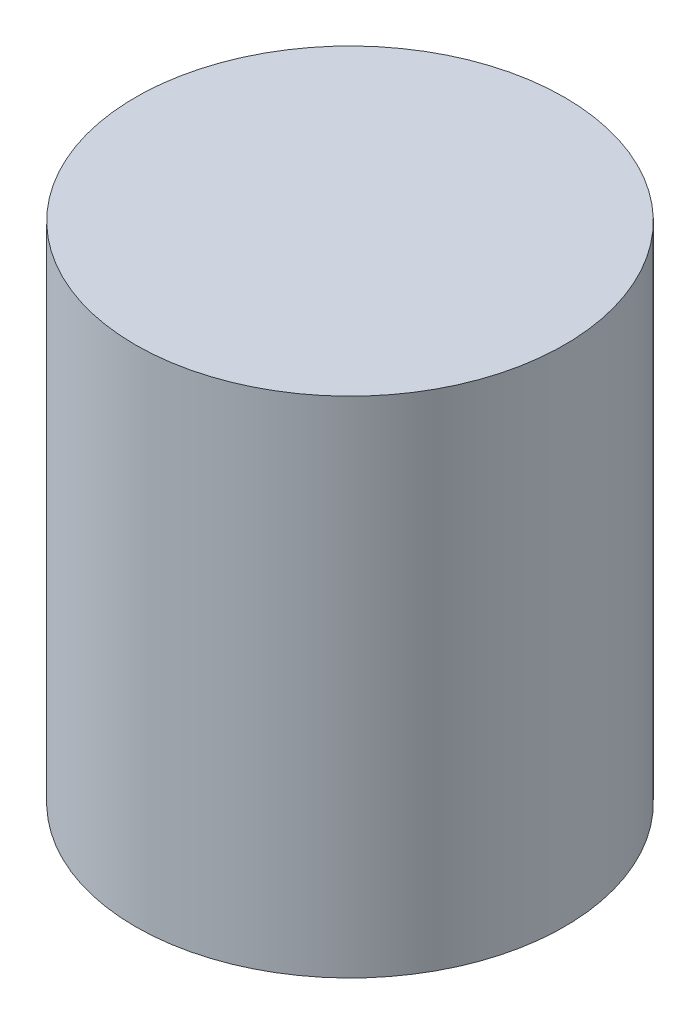
SolidWorks part; units mm, degrees
ref_plane "Alzado" through (0, 0, 0) normal (0, 0, 1) x (1, 0, 0)
ref_plane "Planta" through (0, 0, 0) normal (0, 1, 0) x (1, 0, 0)
ref_plane "Vista lateral" through (0, 0, 0) normal (1, 0, 0) x (0, 0, -1)
sketch "Croquis1" plane through (0, 0, 0) normal (0, 1, 0) x (1, 0, 0)
  circle A0 centre (0, 0) radius 63
extrude "Saliente-Extruir1" add sketch "Croquis1" along normal blind 145
sketch "Croquis2" plane through (0, 145, 0) normal (0, 1, 0) x (1, 0, 0)
  circle A0 centre (0, 0) radius 60
  circle A1 centre (0, 0) radius 63 construction
  dimension "D1" = 3
extrude "Cortar-Extruir1" cut sketch "Croquis2" against normal blind 142 and the other way blind 2
sketch "Croquis3" plane through (0, 145, 0) normal (0, 1, 0) x (1, 0, 0)
  circle A0 centre (0, 0) radius 63
extrude "Saliente-Extruir2" add sketch "Croquis3" along normal blind 3
